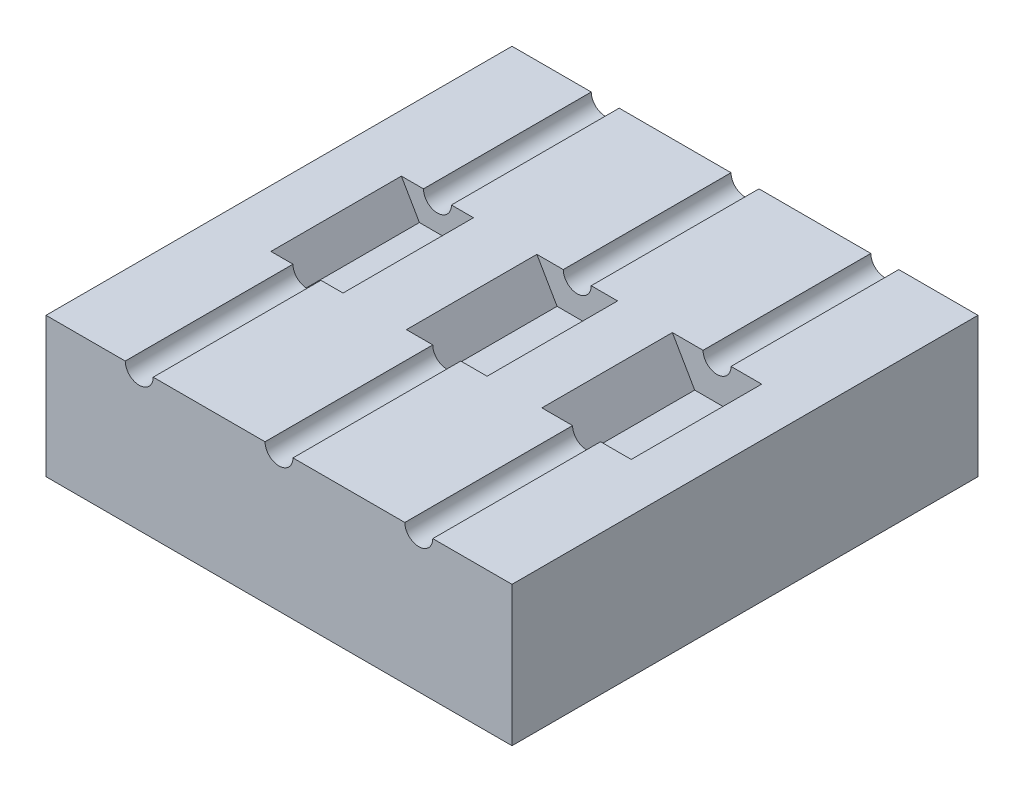
SolidWorks part; units mm, degrees
ref_plane "Front Plane" through (0, 0, 0) normal (0, 0, 1) x (1, 0, 0)
ref_plane "Top Plane" through (0, 0, 0) normal (0, 1, 0) x (1, 0, 0)
ref_plane "Right Plane" through (0, 0, 0) normal (1, 0, 0) x (0, 0, -1)
sketch "Sketch2" plane through (0, 0, 0) normal (0, 1, 0) x (1, 0, 0)
  line L1 (0, 0) -> (25, 0)
  line L2 (0, 0) -> (0, 25)
  line L3 (0, 25) -> (25, 25)
  line L4 (25, 0) -> (25, 25)
  dimension "D1" = 25
  dimension "D2" = 25
extrude "Boss-Extrude1" add sketch "Sketch2" along normal blind 7.5
ref_plane "Plane1" through (0, 0, -12.5) normal (0, 0, 1) x (1, 0, 0)
sketch "Sketch3" plane through (0, 0, -12.5) normal (0, 0, 1) x (1, 0, 0)
  line L0 (4.0329, 5.825) -> (5.9671, 5.825)
  line L1 (5.9671, 5.825) -> (6.9341, 7.5)
  line L2 (0, 7.5) -> (25, 7.5) construction
  line L3 (6.9341, 7.5) -> (3.0659, 7.5)
  line L4 (5, 7.5) -> (5, 0) construction
  line L6 (4.0329, 5.825) -> (3.0659, 7.5)
  line L7 (11.4175, 5.625) -> (13.5825, 5.625)
  line L8 (13.5825, 5.625) -> (14.6651, 7.5)
  line L9 (14.6651, 7.5) -> (10.3349, 7.5)
  line L10 (12.5, 7.5) -> (12.5, 0) construction
  line L11 (11.4175, 5.625) -> (10.3349, 7.5)
  line L12 (0, 0) -> (25, 0) construction
  line L13 (18.802, 5.425) -> (21.198, 5.425)
  line L14 (21.198, 5.425) -> (22.396, 7.5)
  line L15 (22.396, 7.5) -> (17.604, 7.5)
  line L16 (20, 7.5) -> (20, 0) construction
  line L17 (18.802, 5.425) -> (17.604, 7.5)
  line L18 (0, 7.5) -> (0, 0) construction
  line L19 (25, 7.5) -> (25, 0) construction
  point P11 (5, 5.825)
  point P16 (12.5, 5.625)
  point P25 (20, 5.425)
  dimension "D1" = 120
  dimension "D2" = 1.675
  dimension "D3" = 120
  dimension "D4" = 1.875
  dimension "D5" = 120
  dimension "D6" = 2.075
  dimension "D7" = 5
  dimension "D8" = 5
extrude "Cut-Hex" cut sketch "Sketch3" against normal blind 3.5 and the other way blind 3.5
sketch "Sketch4" plane through (0, 0, -9) normal (0, 0, -1) x (-1, 0, 0)
  line L0 (-25, 7.5) -> (0, 7.5) construction
  line L1 (-22.396, 7.5) -> (-17.604, 7.5) construction
  line L2 (-6.9341, 7.5) -> (-3.0659, 7.5) construction
  circle A0 centre (-12.5, 7.5) radius 0.75
  circle A1 centre (-20, 7.5) radius 0.75
  circle A2 centre (-5, 7.5) radius 0.75
  dimension "D1" = 1.5
extrude "Cut-Cable Exit" cut sketch "Sketch4" against normal through all and the other way through all
